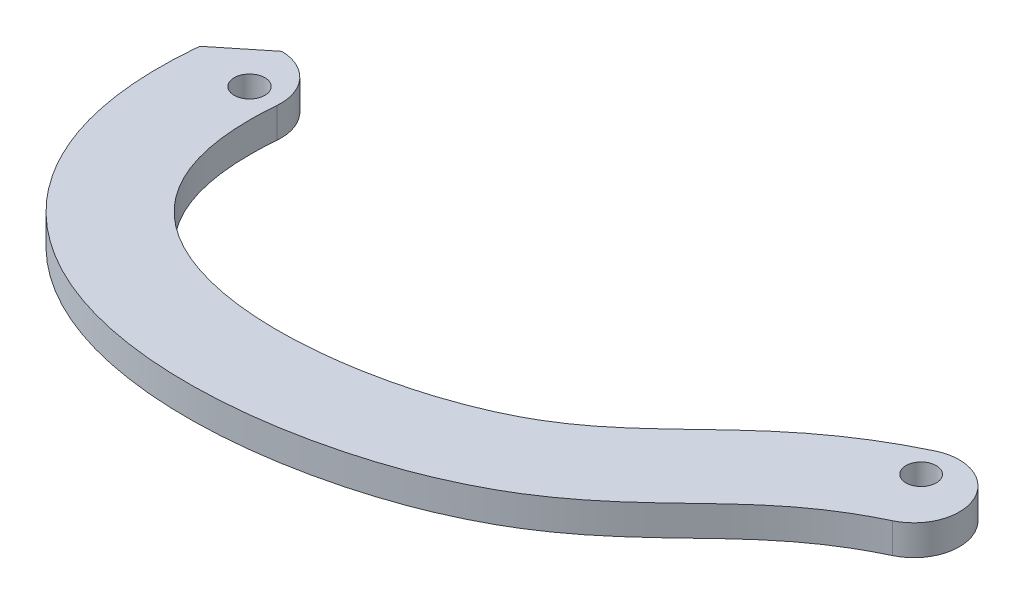
SolidWorks part; units mm, degrees
ref_plane "Front Plane" through (0, 0, 0) normal (0, 0, 1) x (1, 0, 0)
ref_plane "Top Plane" through (0, 0, 0) normal (0, 1, 0) x (1, 0, 0)
ref_plane "Right Plane" through (0, 0, 0) normal (1, 0, 0) x (0, 0, -1)
sketch "Sketch1" plane through (0, 0, 0) normal (0, 1, 0) x (1, 0, 0)
  line L0 (35.306, 0) -> (-35.306, 0) construction
  circle A0 centre (-35.306, 0) radius 1.6129
  circle A1 centre (35.306, 0) radius 1.5875
  arc A2 (-32.1428, -0.2734) -> (-41.6324, 0.5468) centre (-36.8876, 0.1367) ccw
  arc A3 (38.0356, -5.7334) -> (33.9412, 2.8667) centre (35.9884, -1.4333) ccw
  spline S0 degree 3 poles (35.306, 0) (23.2173, -5.7552) (16.0545, -25.5319) (-37.7774, -28.5933) (-35.306, 0) knots 0 0 0 0 0.399142 1 1 1 1 construction
  spline S1 degree 1 poles (33.9412, 2.8667) (-32.1428, -0.2734) knots 0 0 1 1 construction
  spline S2 degree 3 poles (33.9412, 2.8667) (33.4449, 2.6304) (32.4467, 2.1338) (30.5935, 1.129) (28.4545, -0.1799) (26.1588, -1.801) (23.3976, -4.0002) (20.4088, -6.7512) (17.1995, -9.8717) (13.9933, -12.7004) (10.992, -14.7963) (8.1667, -16.3135) (4.9567, -17.7336) (0.3637, -19.2503) (-5.6728, -20.4565) (-11.8371, -20.8832) (-17.7298, -20.3929) (-22.9525, -18.8931) (-26.4626, -16.7907) (-28.6984, -14.5679) (-30.0909, -12.5912) (-31.1867, -10.2453) (-31.8225, -7.9254) (-32.1351, -5.8212) (-32.2631, -4.1149) (-32.2735, -2.579) (-32.2205, -1.288) (-32.1717, -0.6084) (-32.1428, -0.2734) knots 0 0 0 0 0.015625 0.03125 0.0625 0.09375 0.125 0.1875 0.25 0.3125 0.375 0.40625 0.4375 0.5 0.5625 0.625 0.6875 0.75 0.8125 0.84375 0.875 0.90625 0.9375 0.953125 0.96875 0.984375 0.992188 1 1 1 1
  spline S3 degree 1 poles (38.0356, -5.7334) (-41.6324, 0.5468) knots 0 0 1 1 construction
  spline S4 degree 3 poles (38.0356, -5.7334) (37.6385, -5.9225) (36.8369, -6.3213) (35.3711, -7.1163) (33.6932, -8.1432) (31.8839, -9.4202) (29.6484, -11.1987) (27.036, -13.5928) (22.68, -17.8315) (17.2117, -22.4992) (9.3964, -26.3158) (0.5766, -29.2055) (-9.3371, -30.6422) (-19.3303, -29.8406) (-26.6182, -27.8004) (-32.2139, -24.5143) (-36.0147, -20.7449) (-38.3928, -17.3646) (-40.1925, -13.4871) (-41.3554, -9.1921) (-41.7826, -5.3005) (-41.8043, -2.0285) (-41.7058, -0.3023) (-41.6324, 0.5468) knots 0 0 0 0 0.015625 0.03125 0.0625 0.09375 0.125 0.1875 0.25 0.375 0.4375 0.5 0.625 0.6875 0.75 0.8125 0.84375 0.875 0.90625 0.9375 0.96875 0.984375 1 1 1 1
  dimension "D1" = 70.612
  dimension "D2" = 3.2258
  dimension "D3" = 3.175
  dimension "D4" = 3.175
  dimension "D6" = 6.35
extrude "Boss-Extrude1" add sketch "Sketch1" along normal blind 3.175
sketch "Sketch3" plane through (0, 3.175, 0) normal (0, 1, 0) x (1, 0, 0)
  line L0 (-41.5566, 1.0758) -> (-36.8191, 4.8987)
  line L1 (-35.306, 0) -> (-38.2968, 3.7063) construction
  line L2 (-38.2968, 3.7063) -> (-35.4004, 3.7063) construction
  arc A0 (-32.1428, -0.2734) -> (-41.6324, 0.5468) centre (-36.8876, 0.1367) ccw construction
  arc A1 (-36.8191, 4.8987) -> (-41.5566, 1.0758) centre (-36.8876, 0.1367) ccw
  circle A2 centre (-35.306, 0) radius 1.6129 construction
  dimension "D1" = 4.7625
  dimension "D2" = 38.902
extrude "Cut-Extrude1" cut sketch "Sketch3" against normal up to next
